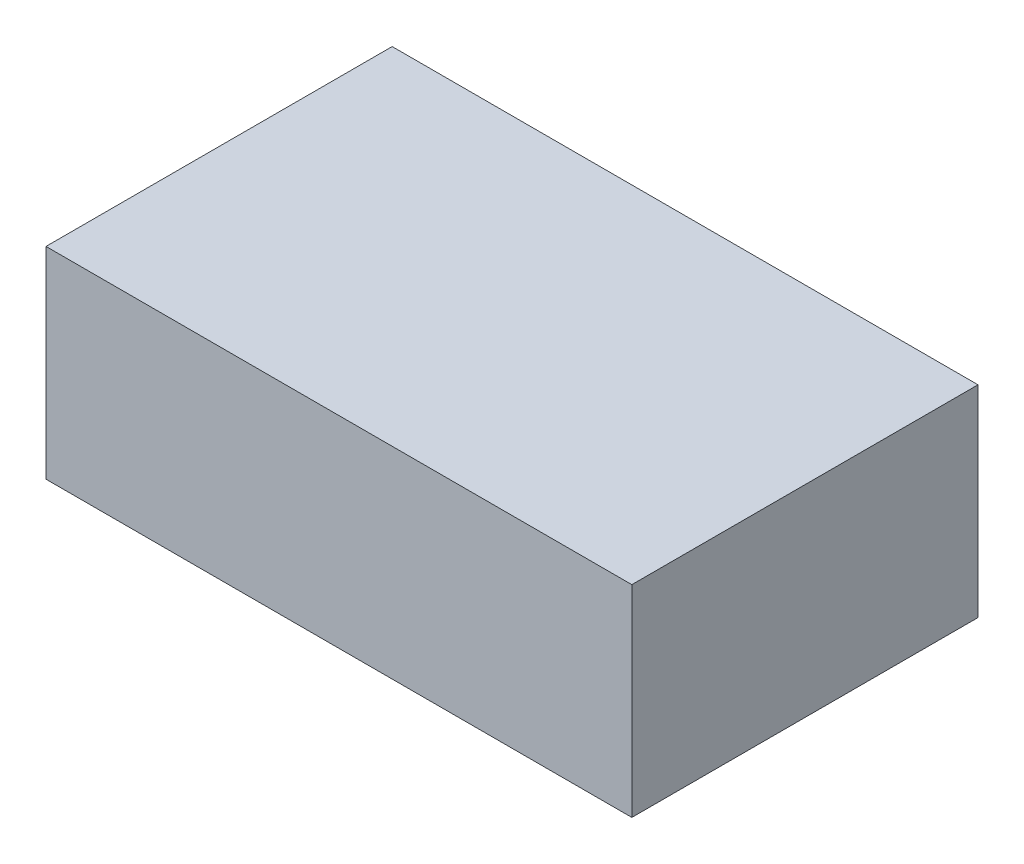
SolidWorks part; units mm, degrees
ref_plane "前视基准面" through (0, 0, 0) normal (0, 0, 1) x (1, 0, 0)
ref_plane "上视基准面" through (0, 0, 0) normal (0, 1, 0) x (1, 0, 0)
ref_plane "右视基准面" through (0, 0, 0) normal (1, 0, 0) x (0, 0, -1)
sketch "草图1" plane through (0, 0, 0) normal (0, 1, 0) x (1, 0, 0)
  line L1 (-77, -45.5) -> (77, -45.5)
  line L2 (-77, -45.5) -> (-77, 45.5)
  line L3 (-77, 45.5) -> (77, 45.5)
  line L4 (77, -45.5) -> (77, 45.5)
  line L5 (-77, -45.5) -> (77, 45.5) construction
  line L6 (-77, 45.5) -> (77, -45.5) construction
  point P0 (0, 0)
  dimension "D1" = 91
  dimension "D2" = 154
extrude "凸台-拉伸1" add sketch "草图1" along normal blind 53
